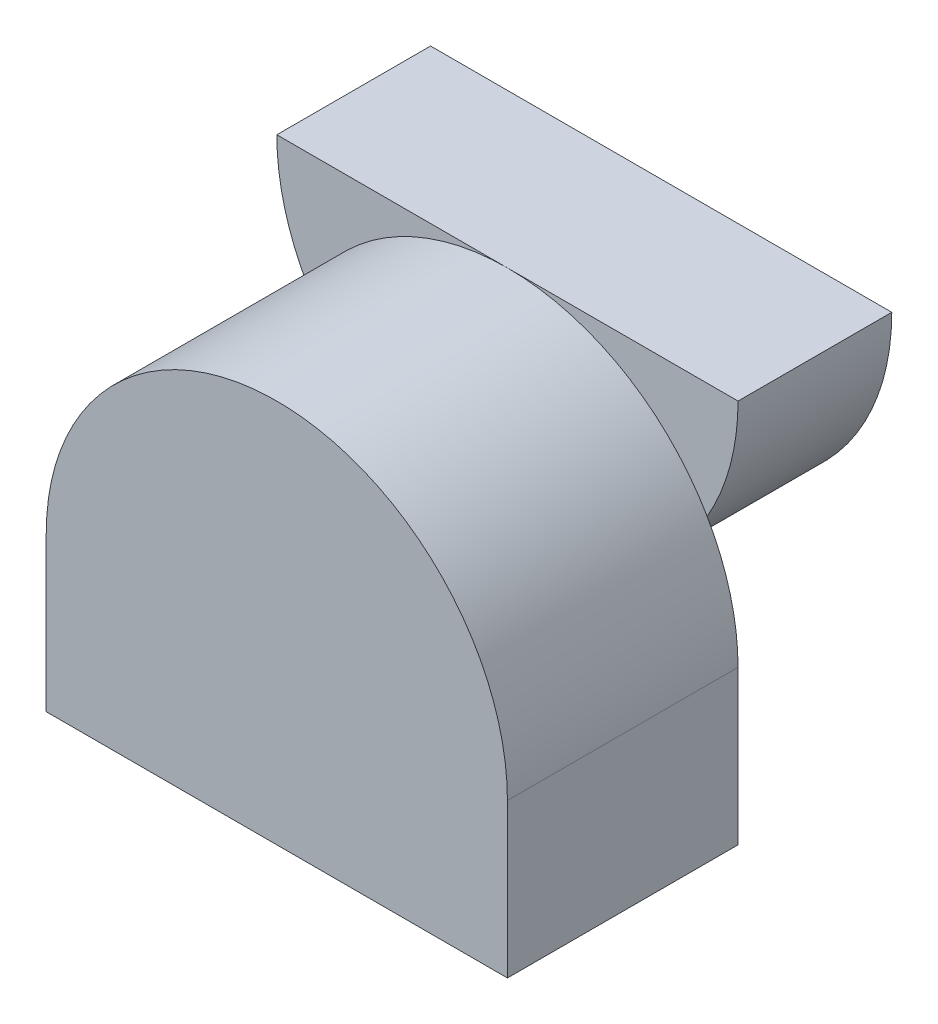
SolidWorks part; units mm, degrees
ref_plane "Front Plane" through (0, 0, 0) normal (0, 0, 1) x (1, 0, 0)
ref_plane "Top Plane" through (0, 0, 0) normal (0, 1, 0) x (1, 0, 0)
ref_plane "Right Plane" through (0, 0, 0) normal (1, 0, 0) x (0, 0, -1)
sketch "Sketch1" plane through (0, 0, 0) normal (0, 0, 1) x (1, 0, 0)
  line L0 (-30, 10) -> (-30, 0)
  line L1 (-30, 0) -> (0, 0)
  line L2 (0, 0) -> (0, 10)
  arc A0 (0, 10) -> (-30, 10) centre (-15, 10) ccw
  dimension "D1" = 10
  dimension "D2" = 30
extrude "Boss-Extrude2" add sketch "Sketch1" along normal blind 15
sketch "Sketch2" plane through (0, 0, 0) normal (0, 0, -1) x (-1, 0, 0)
  line L0 (0, 25) -> (30, 25)
  line L1 (30, 0) -> (0, 0) construction
  arc A0 (30, 25) -> (0, 25) centre (15, 25) cw
  dimension "D1" = 25
extrude "Boss-Extrude3" add sketch "Sketch2" along normal blind 10
